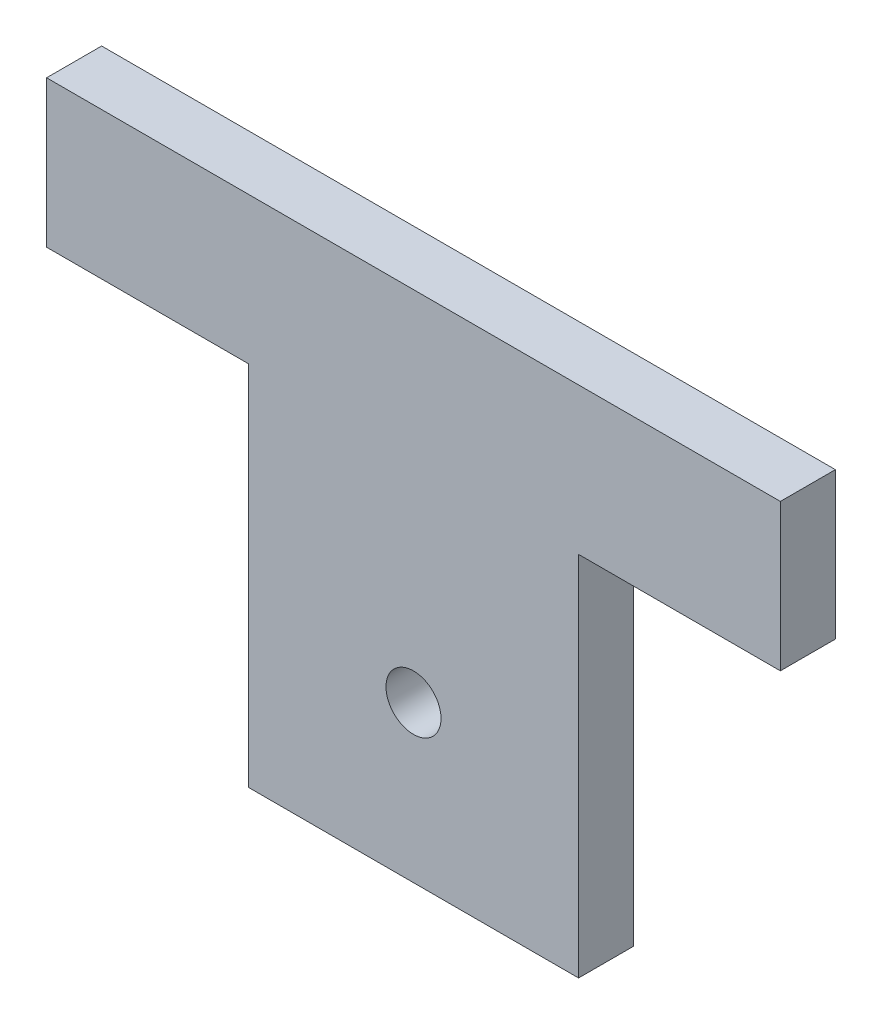
SolidWorks part; units mm, degrees
material "Acrylic (Medium-high impact)"
ref_plane "Front Plane" through (0, 0, 0) normal (0, 0, 1) x (1, 0, 0)
ref_plane "Top Plane" through (0, 0, 0) normal (0, 1, 0) x (1, 0, 0)
ref_plane "Right Plane" through (0, 0, 0) normal (1, 0, 0) x (0, 0, -1)
sketch "Sketch1" plane through (0, 0, 0) normal (0, 0, 1) x (1, 0, 0)
  line L0 (0, 46.0711) -> (0, -47.5009) construction
  line L1 (-42.7538, 0) -> (46.296, 0) construction
  line L2 (20, 8) -> (-20, 8)
  line L3 (-20, 8) -> (-20, 0)
  line L4 (-20, 0) -> (-9, 0)
  line L5 (-9, 0) -> (-9, -20)
  line L6 (-9, -20) -> (9, -20)
  line L7 (9, 0) -> (9, -20)
  line L8 (20, 0) -> (9, 0)
  line L9 (20, 8) -> (20, 0)
  line L10 (-26.8383, -3) -> (23.659, -3) construction
  circle A0 centre (0, -11.5) radius 1.5
  point P12 (0, 8)
  point P13 (0, -20)
  point P17 (14.5, 0)
  dimension "D6" = 3
  dimension "D1" = 18
  dimension "D2" = 8
  dimension "D3" = 40
  dimension "D4" = 20
  dimension "D5" = 3
  dimension "D7" = 8.5
extrude "Boss-Extrude1" add sketch "Sketch1" along normal blind 3
